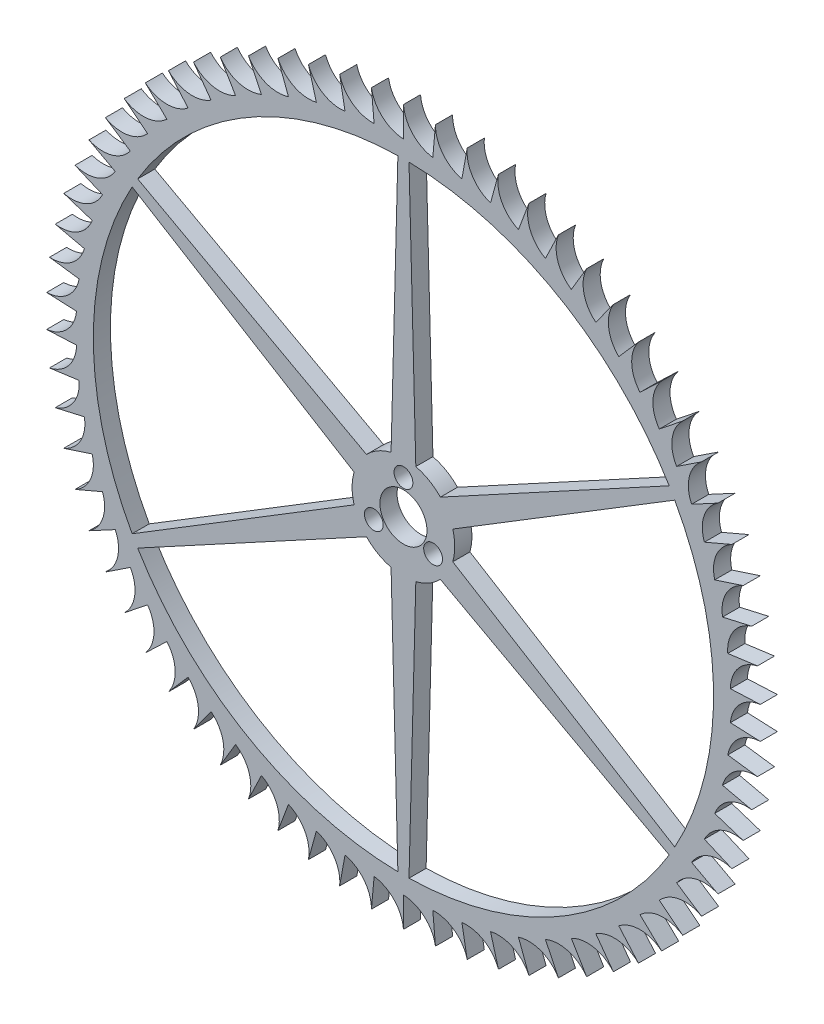
SolidWorks part; units mm, degrees
ref_plane "Front Plane" through (0, 0, 0) normal (0, 0, 1) x (1, 0, 0)
ref_plane "Top Plane" through (0, 0, 0) normal (0, 1, 0) x (1, 0, 0)
ref_plane "Right Plane" through (0, 0, 0) normal (1, 0, 0) x (0, 0, -1)
sketch "Sketch1" plane through (0, 0, 0) normal (0, 0, 1) x (1, 0, 0)
  line L0 (-27.5, 98.2479) -> (-27.5, 101.7479)
  line L1 (-27.5, 98.2479) -> (-27.5, 96.2479) construction
  circle A0 centre (-27.5, 59.9979) radius 40 construction
  circle A1 centre (-27.5, 59.9979) radius 40 construction
  circle A2 centre (-27.5, 59.9979) radius 36.25
  circle A3 centre (-27.5, 59.9979) radius 38.25
  arc A4 (-27.5, 101.7479) -> (-23.8897, 98.0772) centre (-23.5121, 102.0593) ccw
  point P9 (-27.5, 99.9979)
  dimension "D1" = 2
  dimension "D3" = 4
  dimension "D2" = 3.5
extrude "Boss-Extrude1" add sketch "Sketch1" against normal up to vertex (2 mm away) contours A4 L0 A3 | A3 A2
pattern_circular "CirPattern1" count 70 over 360 about axis through (-27.5, 59.9979, 0) along (0, 0, 1) of "Boss-Extrude1"
sketch "Sketch2" plane through (0, 0, 0) normal (0, 0, 1) x (1, 0, 0)
  line L0 (-27.5, 59.9979) -> (-27.5, 96.2479) construction
  line L1 (-26.85, 96.2479) -> (-28.15, 96.2479)
  line L2 (-28.15, 96.2479) -> (-28.9468, 65.8209)
  line L3 (-26.85, 96.2479) -> (-26.0532, 65.8209)
  circle A0 centre (-27.5, 59.9979) radius 6 construction
  arc A1 (-28.9468, 65.8209) -> (-26.0532, 65.8209) centre (-27.5, 59.9979) ccw
  circle A2 centre (-27.5, 59.9979) radius 36.25 construction
  point P9 (-27.5, 96.2479)
  dimension "D1" = 1.3
  dimension "D2" = 1.5
extrude "Boss-Extrude2" add sketch "Sketch2" against normal up to surface (2 mm away) up to face at (-27.5, 59.9979, -2)
pattern_circular "CirPattern3" count 6 over 360 about axis through (-27.5, 59.9979, 0) along (0, 0, 1) of "Boss-Extrude2"
hole_wizard "M2 Clearance Hole1" positions "Sketch3" profile "Sketch4" hole size "M2" standard "ANSI Metric" end condition through all
sketch "Sketch3" plane through (0, 0, 0) normal (0, 0, 1) x (1, 0, 0)
  point P0 (-27.5, 63.9979)
  point P3 (-30.9641, 57.9979)
  point P6 (-24.0359, 57.9979)
sketch "Sketch4" plane through (-27.5, 63.9979, 0) normal (1, 0, 0) x (0, -1, 0)
  line L0 (0, 0) -> (0, 2)
  line L1 (0, 2) -> (1.1, 2)
  line L2 (1.1, 2) -> (1.1, 0)
  line L5 (1.1, 0) -> (0, 0)
  line L11 (0, -6.35) -> (0, 107.95) construction
  dimension "Thru Hole Dia." = 2.2
  dimension "Thru Hole Depth" = 2
sketch "Sketch6" plane through (0, 0, 0) normal (0, 0, 1) x (1, 0, 0)
  circle A0 centre (-27.5, 59.9979) radius 2.75 construction
  circle A1 centre (-27.5, 59.9979) radius 2.75
extrude "Cut-Extrude1" cut sketch "Sketch6" against normal through all
